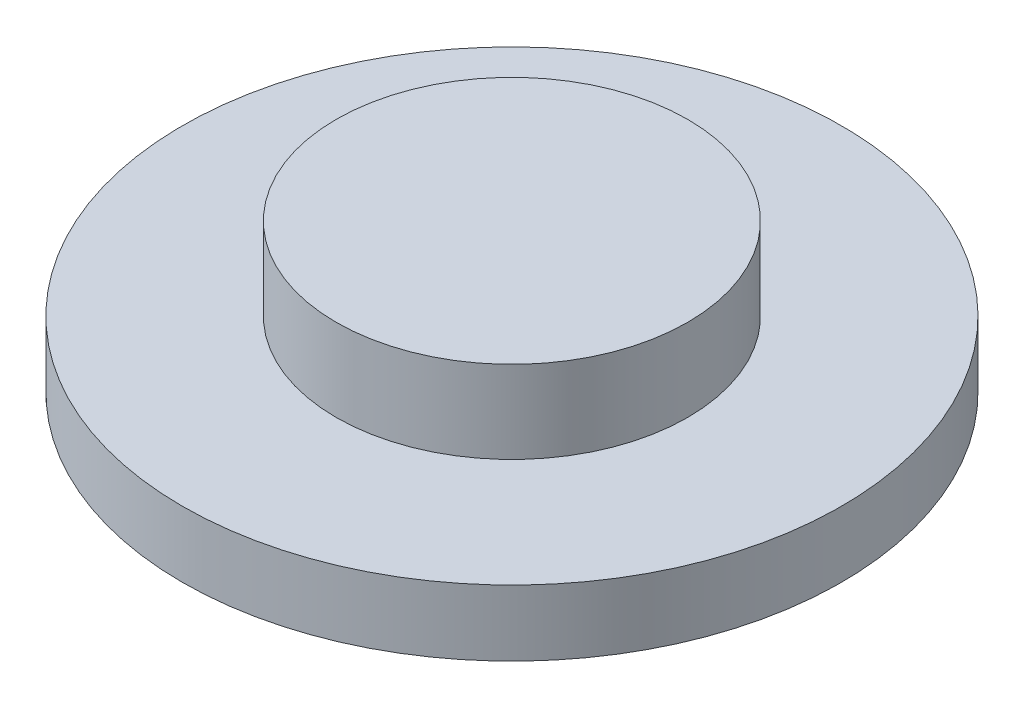
SolidWorks part; units mm, degrees
ref_plane "前视基准面" through (0, 0, 0) normal (0, 0, 1) x (1, 0, 0)
ref_plane "上视基准面" through (0, 0, 0) normal (0, 1, 0) x (1, 0, 0)
ref_plane "右视基准面" through (0, 0, 0) normal (1, 0, 0) x (0, 0, -1)
other "Configuration Table"
sketch "草图1" plane through (0, 0, 0) normal (0, 1, 0) x (1, 0, 0)
  circle A0 centre (0, 0) radius 15
  dimension "D1" = 30
extrude "凸台-拉伸1" add sketch "草图1" along normal blind 3
sketch "草图2" plane through (0, 3, 0) normal (0, 1, 0) x (1, 0, 0)
  circle A0 centre (0, 0) radius 8
  dimension "D1" = 16
extrude "凸台-拉伸2" add sketch "草图2" along normal blind 3.75
